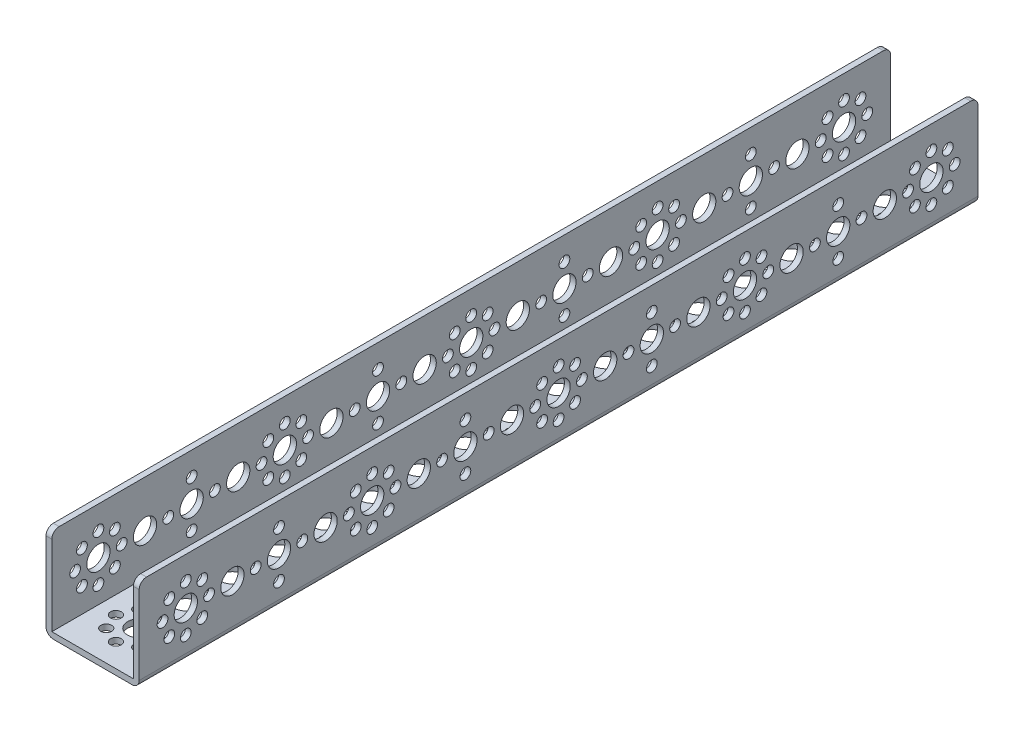
SolidWorks part; units mm, degrees
material "2024 Alloy"
ref_plane "Front Plane" through (0, 0, 0) normal (0, 0, 1) x (1, 0, 0)
ref_plane "Top Plane" through (0, 0, 0) normal (0, 1, 0) x (1, 0, 0)
ref_plane "Right Plane" through (0, 0, 0) normal (1, 0, 0) x (0, 0, -1)
ref_plane "Plane1" through (16, 0, 0) normal (1, 0, 0) x (0, 0, -1)
sketch "Sketch1" plane through (16, 0, 0) normal (1, 0, 0) x (0, 0, -1)
  line L0 (-16, 32) -> (-16, 0)
  line L1 (-16, 0) -> (272, 0)
  line L2 (272, 0) -> (272, 32)
  line L3 (272, 32) -> (-16, 32)
extrude "Boss-Extrude1" add sketch "Sketch1" against normal blind 32
sketch "Sketch2" plane through (0, 0, -272) normal (0, 0, -1) x (-1, 0, 0)
  line L0 (14, 32) -> (-14, 32)
  line L1 (-14, 32) -> (-14, 2)
  line L2 (-14, 2) -> (14, 2)
  line L3 (14, 2) -> (14, 32)
extrude "Cut-Extrude1" cut sketch "Sketch2" against normal through all
hole_wizard "Ø8.0 (8) Diameter Hole1" positions "Sketch4" profile "Sketch3" hole size "Ø8.0" standard "ANSI Metric"
sketch "Sketch4" plane through (-16, 0, 0) normal (-1, 0, 0) x (0, 0, 1)
  point P0 (-64, 16)
  point P1 (-128, 16)
  point P2 (-192, 16)
  point P3 (-256, 16)
  point P4 (-32, 16)
  point P5 (-96, 16)
  point P6 (-160, 16)
  point P7 (-224, 16)
  point P8 (-16, 16)
  point P9 (-48, 16)
  point P10 (-80, 16)
  point P11 (-112, 16)
  point P12 (0, 16)
  point P13 (-144, 16)
  point P14 (-176, 16)
  point P15 (-208, 16)
  point P16 (-240, 16)
sketch "Sketch3" plane through (-16, 16, -64) normal (0, 1, 0) x (0, 0, 1)
  line L0 (0, 0) -> (0, 2)
  line L1 (0, 2) -> (4, 2)
  line L2 (4, 2) -> (4, 0)
  line L5 (4, 0) -> (0, 0)
  line L11 (0, -6.35) -> (0, 107.95) construction
  dimension "Thru Hole Dia." = 8
  dimension "Thru Hole Depth" = 2
hole_wizard "Ø3.7 (3.7) Diameter Hole1" positions "Sketch6" profile "Sketch5" hole size "Ø3.7" standard "ANSI Metric"
sketch "Sketch6" plane through (-16, 0, 0) normal (-1, 0, 0) x (0, 0, 1)
  point P0 (0, 24)
  point P1 (0, 8)
  point P2 (-8, 16)
  point P3 (8, 16)
  point P4 (-5.6569, 21.6569)
  point P5 (5.6569, 21.6569)
  point P6 (5.6569, 10.3431)
  point P7 (-5.6569, 10.3431)
  point P8 (-64, 24)
  point P9 (-64, 8)
  point P10 (-72, 16)
  point P11 (-56, 16)
  point P12 (-69.6569, 21.6569)
  point P13 (-58.3431, 21.6569)
  point P14 (-58.3431, 10.3431)
  point P15 (-69.6569, 10.3431)
  point P16 (-128, 24)
  point P17 (-128, 8)
  point P18 (-136, 16)
  point P19 (-120, 16)
  point P20 (-133.6569, 21.6569)
  point P21 (-122.3431, 21.6569)
  point P22 (-122.3431, 10.3431)
  point P23 (-133.6569, 10.3431)
  point P24 (-192, 24)
  point P25 (-192, 8)
  point P26 (-200, 16)
  point P27 (-184, 16)
  point P28 (-197.6569, 21.6569)
  point P29 (-186.3431, 21.6569)
  point P30 (-186.3431, 10.3431)
  point P31 (-197.6569, 10.3431)
  point P32 (-256, 24)
  point P33 (-256, 8)
  point P34 (-264, 16)
  point P35 (-248, 16)
  point P36 (-261.6569, 21.6569)
  point P37 (-250.3431, 21.6569)
  point P38 (-250.3431, 10.3431)
  point P39 (-261.6569, 10.3431)
  point P40 (-32, 24)
  point P41 (-40, 16)
  point P42 (-32, 8)
  point P43 (-24, 16)
  point P44 (-96, 24)
  point P45 (-104, 16)
  point P46 (-96, 8)
  point P47 (-88, 16)
  point P48 (-160, 24)
  point P49 (-168, 16)
  point P50 (-160, 8)
  point P51 (-152, 16)
  point P52 (-224, 24)
  point P53 (-232, 16)
  point P54 (-224, 8)
  point P55 (-216, 16)
sketch "Sketch5" plane through (-16, 24, 0) normal (0, 1, 0) x (0, 0, 1)
  line L0 (0, 0) -> (0, 2)
  line L1 (0, 2) -> (1.85, 2)
  line L2 (1.85, 2) -> (1.85, 0)
  line L5 (1.85, 0) -> (0, 0)
  line L11 (0, -6.35) -> (0, 107.95) construction
  dimension "Thru Hole Dia." = 3.7
  dimension "Thru Hole Depth" = 2
hole_wizard "Ø3.7 (3.7) Diameter Hole2" positions "Sketch8" profile "Sketch7" hole size "Ø3.7" standard "ANSI Metric"
sketch "Sketch8" plane through (0, 0, 0) normal (0, -1, 0) x (-1, 0, 0)
  point P0 (8, 0)
  point P1 (5.6569, 5.6569)
  point P2 (0, 8)
  point P3 (-5.6569, 5.6569)
  point P4 (-8, 0)
  point P5 (-5.6569, -5.6569)
  point P6 (0, -8)
  point P7 (5.6569, -5.6569)
  point P8 (8, 64)
  point P9 (5.6569, 69.6569)
  point P10 (0, 72)
  point P11 (-5.6569, 69.6569)
  point P12 (-8, 64)
  point P13 (-5.6569, 58.3431)
  point P14 (0, 56)
  point P15 (5.6569, 58.3431)
  point P16 (8, 128)
  point P17 (5.6569, 133.6569)
  point P18 (0, 136)
  point P19 (-5.6569, 133.6569)
  point P20 (-8, 128)
  point P21 (-5.6569, 122.3431)
  point P22 (0, 120)
  point P23 (5.6569, 122.3431)
  point P24 (8, 192)
  point P25 (5.6569, 197.6569)
  point P26 (0, 200)
  point P27 (-5.6569, 197.6569)
  point P28 (-8, 192)
  point P29 (-5.6569, 186.3431)
  point P30 (0, 184)
  point P31 (5.6569, 186.3431)
  point P32 (8, 256)
  point P33 (5.6569, 261.6569)
  point P34 (0, 264)
  point P35 (-5.6569, 261.6569)
  point P36 (-8, 256)
  point P37 (-5.6569, 250.3431)
  point P38 (0, 248)
  point P39 (5.6569, 250.3431)
  point P40 (8, 32)
  point P41 (0, 40)
  point P42 (-8, 32)
  point P43 (0, 24)
  point P44 (8, 96)
  point P45 (0, 104)
  point P46 (-8, 96)
  point P47 (0, 88)
  point P48 (8, 160)
  point P49 (0, 168)
  point P50 (-8, 160)
  point P51 (0, 152)
  point P52 (8, 224)
  point P53 (0, 232)
  point P54 (-8, 224)
  point P55 (0, 216)
sketch "Sketch7" plane through (-8, 0, 0) normal (1, 0, 0) x (0, 0, -1)
  line L0 (0, 0) -> (0, 32)
  line L1 (0, 32) -> (1.85, 32)
  line L2 (1.85, 32) -> (1.85, 0)
  line L5 (1.85, 0) -> (0, 0)
  line L11 (0, -6.35) -> (0, 107.95) construction
  dimension "Thru Hole Dia." = 3.7
  dimension "Thru Hole Depth" = 32
hole_wizard "Ø8.0 (8) Diameter Hole2" positions "Sketch10" profile "Sketch9" hole size "Ø8.0" standard "ANSI Metric"
sketch "Sketch10" plane through (0, 0, 0) normal (0, -1, 0) x (-1, 0, 0)
  point P0 (0, 0)
  point P1 (0, 64)
  point P2 (0, 128)
  point P3 (0, 192)
  point P4 (0, 256)
  point P5 (0, 32)
  point P6 (0, 96)
  point P7 (0, 160)
  point P8 (0, 224)
  point P9 (0, 16)
  point P10 (0, 48)
  point P11 (0, 80)
  point P12 (0, 112)
  point P13 (0, 144)
  point P14 (0, 176)
  point P15 (0, 208)
  point P16 (0, 240)
sketch "Sketch9" plane through (0, 0, 0) normal (1, 0, 0) x (0, 0, -1)
  line L0 (0, 0) -> (0, 32)
  line L1 (0, 32) -> (4, 32)
  line L2 (4, 32) -> (4, 0)
  line L5 (4, 0) -> (0, 0)
  line L11 (0, -6.35) -> (0, 107.95) construction
  dimension "Thru Hole Dia." = 8
  dimension "Thru Hole Depth" = 32
hole_wizard "Ø8.0 (8) Diameter Hole3" positions "Sketch12" profile "Sketch11" hole size "Ø8.0" standard "ANSI Metric"
sketch "Sketch12" plane through (14, 0, 0) normal (-1, 0, 0) x (0, 0, 1)
  point P0 (-32, 16)
sketch "Sketch11" plane through (14, 16, -32) normal (0, 1, 0) x (0, 0, 1)
  line L0 (0, 0) -> (0, 2)
  line L1 (0, 2) -> (4, 2)
  line L2 (4, 2) -> (4, 0)
  line L5 (4, 0) -> (0, 0)
  line L11 (0, -6.35) -> (0, 107.95) construction
  dimension "Thru Hole Dia." = 8
  dimension "Thru Hole Depth" = 2
hole_wizard "Ø8.0 (8) Diameter Hole4" positions "Sketch14" profile "Sketch13" hole size "Ø8.0" standard "ANSI Metric"
sketch "Sketch14" plane through (16, 0, 0) normal (1, 0, 0) x (0, 0, -1)
  point P0 (64, 16)
  point P1 (128, 16)
  point P2 (192, 16)
  point P3 (256, 16)
  point P4 (96, 16)
  point P5 (160, 16)
  point P6 (224, 16)
  point P7 (16, 16)
  point P8 (48, 16)
  point P9 (80, 16)
  point P10 (112, 16)
  point P11 (0, 16)
  point P12 (144, 16)
  point P13 (176, 16)
  point P14 (208, 16)
  point P15 (240, 16)
sketch "Sketch13" plane through (16, 16, -64) normal (0, 1, 0) x (0, 0, -1)
  line L0 (0, 0) -> (0, 32)
  line L1 (0, 32) -> (4, 32)
  line L2 (4, 32) -> (4, 0)
  line L5 (4, 0) -> (0, 0)
  line L11 (0, -6.35) -> (0, 107.95) construction
  dimension "Thru Hole Dia." = 8
  dimension "Thru Hole Depth" = 32
hole_wizard "Ø3.7 (3.7) Diameter Hole3" positions "Sketch16" profile "Sketch15" hole size "Ø3.7" standard "ANSI Metric"
sketch "Sketch16" plane through (16, 0, 0) normal (1, 0, 0) x (0, 0, -1)
  point P0 (0, 24)
  point P1 (0, 8)
  point P2 (8, 16)
  point P3 (-8, 16)
  point P4 (5.6569, 21.6569)
  point P5 (-5.6569, 21.6569)
  point P6 (-5.6569, 10.3431)
  point P7 (5.6569, 10.3431)
  point P8 (64, 24)
  point P9 (64, 8)
  point P10 (72, 16)
  point P11 (56, 16)
  point P12 (69.6569, 21.6569)
  point P13 (58.3431, 21.6569)
  point P14 (58.3431, 10.3431)
  point P15 (69.6569, 10.3431)
  point P16 (128, 24)
  point P17 (128, 8)
  point P18 (136, 16)
  point P19 (120, 16)
  point P20 (133.6569, 21.6569)
  point P21 (122.3431, 21.6569)
  point P22 (122.3431, 10.3431)
  point P23 (133.6569, 10.3431)
  point P24 (192, 24)
  point P25 (192, 8)
  point P26 (200, 16)
  point P27 (184, 16)
  point P28 (197.6569, 21.6569)
  point P29 (186.3431, 21.6569)
  point P30 (186.3431, 10.3431)
  point P31 (197.6569, 10.3431)
  point P32 (256, 24)
  point P33 (256, 8)
  point P34 (264, 16)
  point P35 (248, 16)
  point P36 (261.6569, 21.6569)
  point P37 (250.3431, 21.6569)
  point P38 (250.3431, 10.3431)
  point P39 (261.6569, 10.3431)
  point P40 (32, 24)
  point P41 (40, 16)
  point P42 (32, 8)
  point P43 (24, 16)
  point P44 (96, 24)
  point P45 (104, 16)
  point P46 (96, 8)
  point P47 (88, 16)
  point P48 (160, 24)
  point P49 (168, 16)
  point P50 (160, 8)
  point P51 (152, 16)
  point P52 (224, 24)
  point P53 (232, 16)
  point P54 (224, 8)
  point P55 (216, 16)
sketch "Sketch15" plane through (16, 24, 0) normal (0, 1, 0) x (0, 0, -1)
  line L0 (0, 0) -> (0, 32)
  line L1 (0, 32) -> (1.85, 32)
  line L2 (1.85, 32) -> (1.85, 0)
  line L5 (1.85, 0) -> (0, 0)
  line L11 (0, -6.35) -> (0, 107.95) construction
  dimension "Thru Hole Dia." = 3.7
  dimension "Thru Hole Depth" = 32
fillet "Fillet1" radius 2.5 6 edges at (-16, 0, -128) (-15, 32, -272) (-15, 32, 16) (16, 0, -128) (15, 32, 16) (15, 32, -272)
